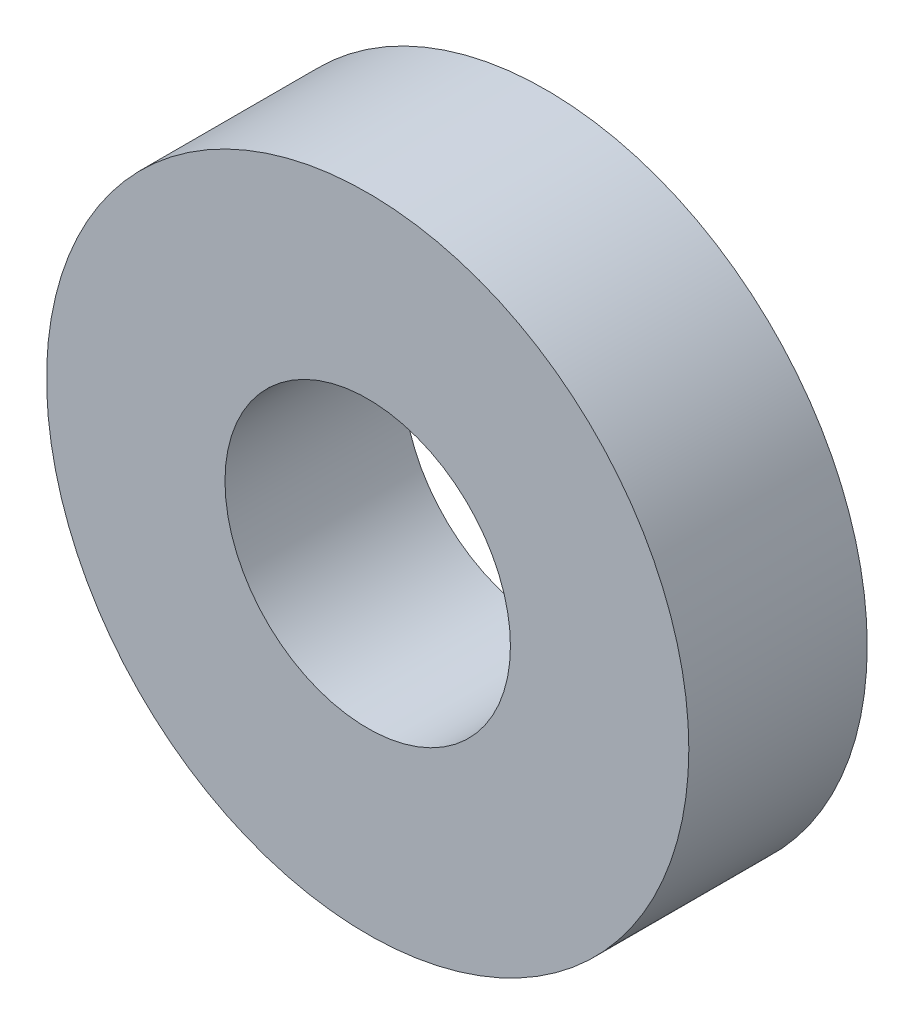
SolidWorks part; units mm, degrees
ref_plane "前视基准面" through (0, 0, 0) normal (0, 0, 1) x (1, 0, 0)
ref_plane "上视基准面" through (0, 0, 0) normal (0, 1, 0) x (1, 0, 0)
ref_plane "右视基准面" through (0, 0, 0) normal (1, 0, 0) x (0, 0, -1)
sketch "草图1" plane through (0, 0, 0) normal (0, 0, 1) x (1, 0, 0)
  circle A0 centre (0, 0) radius 2
  circle A1 centre (0, 0) radius 4.5
extrude "凸台-拉伸1" add sketch "草图1" along normal blind 2.5
